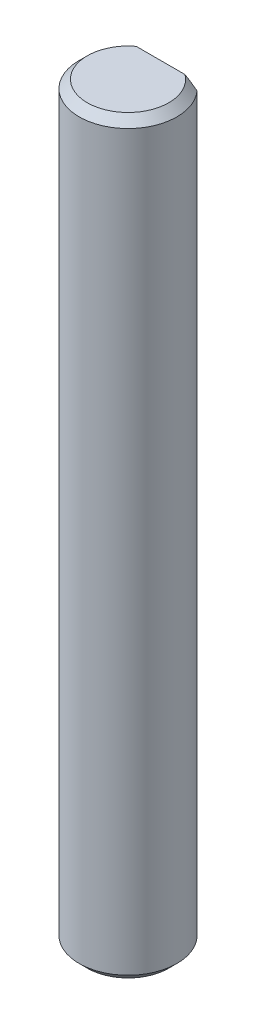
SolidWorks part; units mm, degrees
ref_plane "Front Plane" through (0, 0, 0) normal (0, 0, 1) x (1, 0, 0)
ref_plane "Top Plane" through (0, 0, 0) normal (0, 1, 0) x (1, 0, 0)
ref_plane "Right Plane" through (0, 0, 0) normal (1, 0, 0) x (0, 0, -1)
sketch "Sketch1" plane through (0, 0, 0) normal (0, 1, 0) x (1, 0, 0)
  circle A0 centre (0, 0) radius 3
  dimension "D1" = 6
extrude "Boss-Extrude1" add sketch "Sketch1" along normal blind 46
chamfer "Chamfer1" distance 0.5 angle 45 2 edges at (0, 0, 3) (0, 46, 3)
sketch "Sketch2" plane through (0, 46, 0) normal (0, 1, 0) x (1, 0, 0)
  line L0 (-2.2361, 2) -> (2.2361, 2)
  circle A0 centre (0, 0) radius 3 construction
  arc A1 (2.2361, 2) -> (-2.2361, 2) centre (0, 0) ccw
  dimension "D1" = 2
extrude "Cut-Extrude1" cut sketch "Sketch2" against normal blind 6
sketch "Sketch3" plane through (0, 0, 0) normal (0, -1, 0) x (1, 0, 0)
  line L0 (2.2361, -2) -> (-2.2361, -2)
  circle A0 centre (0, 0) radius 3 construction
  arc A1 (-2.2361, -2) -> (2.2361, -2) centre (0, 0) ccw
  dimension "D1" = 2
extrude "Cut-Extrude2" cut sketch "Sketch3" against normal blind 6
